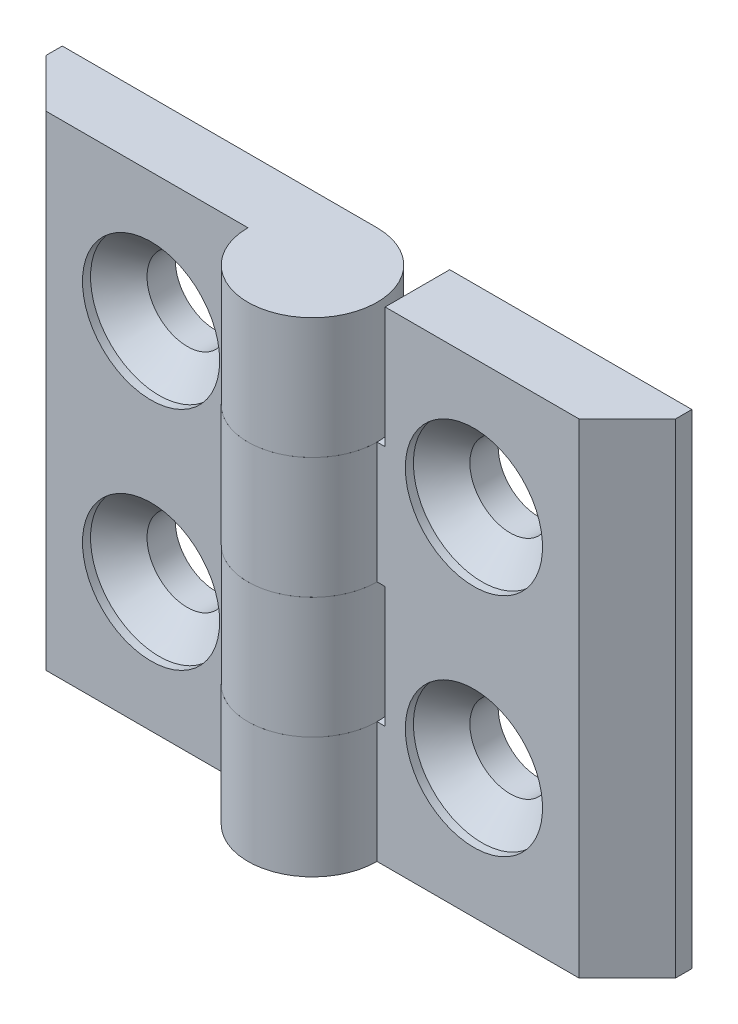
SolidWorks part; units mm, degrees
material "Алюминиевый сплав"
ref_plane "Спереди" through (0, 0, 0) normal (0, 0, 1) x (1, 0, 0)
ref_plane "Сверху" through (0, 0, 0) normal (0, 1, 0) x (1, 0, 0)
ref_plane "Справа" through (0, 0, 0) normal (1, 0, 0) x (0, 0, -1)
sketch "Эскиз1" plane through (0, 0, 0) normal (0, 1, 0) x (1, 0, 0)
  line L0 (0, 4) -> (-19.5, 4)
  line L1 (-19.5, 4) -> (-19.5, 3)
  line L2 (-19.5, 3) -> (-16.5, 0)
  line L3 (-16.5, 0) -> (-4, 0)
  line L4 (0, 0) -> (0, 10.5526) construction
  arc A0 (-4, 0) -> (0, 4) centre (0, 0) ccw
  dimension "D1" = 39
  dimension "D2" = 4
  dimension "D3" = 1
  dimension "D4" = 45
extrude "Бобышка-Вытянуть1" add sketch "Эскиз1" along normal mid plane 30
sketch "Эскиз3" plane through (0, 0, 0) normal (0, 0, 1) x (1, 0, 0)
  line L0 (4, -15) -> (4, 15) construction
  line L1 (-4.5, 7.5) -> (4, 7.5)
  line L2 (-4.5, 7.5) -> (-4.5, 0)
  line L3 (-4.5, 0) -> (4, 0)
  line L4 (4, 7.5) -> (4, 0)
  line L5 (4, 0) -> (4, -7.5) construction
  line L6 (4, -15) -> (-4.5, -15)
  line L7 (4, -15) -> (4, -7.5)
  line L8 (4, -7.5) -> (-4.5, -7.5)
  line L9 (-4.5, -15) -> (-4.5, -7.5)
  line L10 (4, 7.5) -> (4, 15) construction
  line L11 (-4, 15) -> (-4, -15) construction
  dimension "D1" = 0.5
extrude "Вырез-Вытянуть1" cut sketch "Эскиз3" against normal through all and the other way through all
hole_wizard "Зенковка для винта с полупотайной головкой M41" positions "Эскиз4" profile "Эскиз6" countersink size "M4" standard "ISO" end condition through all
sketch "Эскиз4" plane through (0, 0, 0) normal (0, 0, 1) x (1, 0, 0)
  line L0 (-10, 7) -> (-10, -7)
  line L2 (0, 0) -> (0, 18.9001) construction
  line L3 (4, 0) -> (-4, 0) construction
  point P0 (-10, 7)
  point P2 (-10, -7)
  point P9 (-10, 0)
  dimension "D1" = 14
  dimension "D2" = 20
sketch "Эскиз6" plane through (-10, 7, 0) normal (1, 0, 0) x (0, -1, 0)
  line L0 (0, 0) -> (0, 4)
  line L1 (0, 4) -> (2.5, 4)
  line L2 (2.5, 4) -> (2.5, 2.25)
  line L3 (2.5, 2.25) -> (4.25, 0.5)
  line L4 (4.25, 0.5) -> (4.25, 0)
  line L6 (4.25, 0) -> (0, 0)
  line L7 (-2.5, 2.25) -> (-4.25, 0.5) construction
  line L11 (0, -6.35) -> (0, 107.95) construction
  dimension "Диаметр сквозного отверстия" = 5
  dimension "Глубина сквозного отверстия" = 4
  dimension "Диаметр зенковки" = 8.5
  dimension "Угол зенковки" = 90
  dimension "Утопленность" = 0.5
sketch "Угол раскрытия" plane through (0, 0, 0) normal (0, 1, 0) x (1, 0, 0)
  line L0 (0, 0) -> (0, -10)
  line L7 (0, 4) -> (-19.5, 4) construction
  point P3 (-11.2006, -8.7746)
  point P8 (-7.4924, -9.3736)
  point P9 (0, 0)
  point P10 (-11.8016, -2.1731)
  dimension "D1" = 10
  dimension "D2" = 90
pattern_circular "Круговой массив1" count 2 over 360 about axis through (0, 0, 0) along (0, 0, 1) of bodies 106
